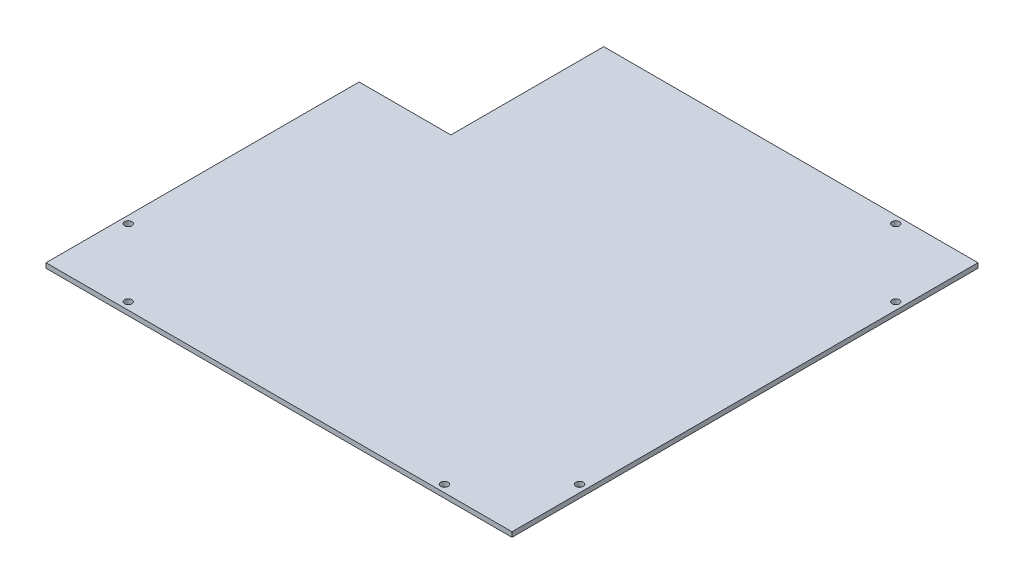
SolidWorks part; units mm, degrees
material "A-Glass Fiber"
ref_plane "Front Plane" through (0, 0, 0) normal (0, 0, 1) x (1, 0, 0)
ref_plane "Top Plane" through (0, 0, 0) normal (0, 1, 0) x (1, 0, 0)
ref_plane "Right Plane" through (0, 0, 0) normal (1, 0, 0) x (0, 0, -1)
sketch "Sketch1" plane through (0, 0, 0) normal (0, 1, 0) x (1, 0, 0)
  line L1 (-76.2, -76.2) -> (76.2, -76.2)
  line L2 (-76.2, -76.2) -> (-76.2, 76.2)
  line L3 (-76.2, 76.2) -> (76.2, 76.2)
  line L4 (76.2, -76.2) -> (76.2, 76.2)
  line L5 (-76.2, -76.2) -> (76.2, 76.2) construction
  line L6 (-76.2, 76.2) -> (76.2, -76.2) construction
  line L8 (-73.8, 76.2) -> (-73.8, -76.2) construction
  line L9 (73.8, 76.2) -> (73.8, -76.2) construction
  line L10 (-76.2, 73.8) -> (76.2, 73.8) construction
  line L11 (-76.2, -73.8) -> (76.2, -73.8) construction
  circle A0 centre (-51.7, 73.8) radius 1.2
  circle A1 centre (51.7, 73.8) radius 1.2
  circle A2 centre (73.8, 51.7) radius 1.2
  circle A3 centre (73.8, -51.7) radius 1.2
  circle A4 centre (-73.8, -51.7) radius 1.2
  circle A5 centre (-73.8, 51.7) radius 1.2
  circle A6 centre (-51.7, -73.8) radius 1.2
  circle A7 centre (51.7, -73.8) radius 1.2
  point P0 (0, 0)
  dimension "D3" = 2.4
  dimension "D1" = 152.4
  dimension "D2" = 152.4
  dimension "D4" = 2.4
  dimension "D5" = 2.4
  dimension "D6" = 2.4
  dimension "D7" = 24.5
  dimension "D8" = 24.5
  dimension "D9" = 2.4
  dimension "D10" = 24.5
  dimension "D11" = 24.5
extrude "Boss-Extrude1" add sketch "Sketch1" along normal blind 1.5748
sketch "Sketch2" plane through (0, 1.5748, 0) normal (0, 1, 0) x (1, 0, 0)
  line L1 (-76.2, 76.2) -> (-46.2, 76.2)
  line L2 (-76.2, 76.2) -> (-76.2, 26.2)
  line L3 (-76.2, 26.2) -> (-46.2, 26.2)
  line L4 (-46.2, 76.2) -> (-46.2, 26.2)
  dimension "D1" = 50
  dimension "D2" = 30
extrude "Cut-Extrude1" cut sketch "Sketch2" against normal through all
